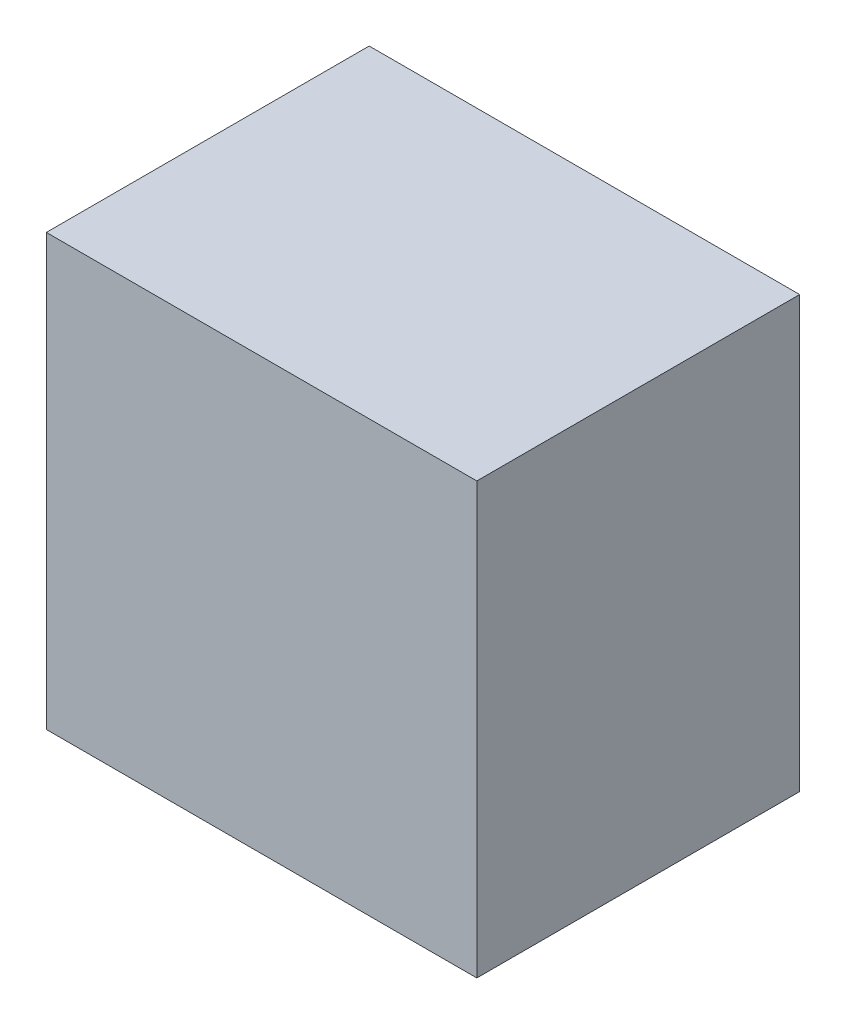
SolidWorks part; units mm, degrees
ref_plane "Front Plane" through (0, 0, 0) normal (0, 0, 1) x (1, 0, 0)
ref_plane "Top Plane" through (0, 0, 0) normal (0, 1, 0) x (1, 0, 0)
ref_plane "Right Plane" through (0, 0, 0) normal (1, 0, 0) x (0, 0, -1)
sketch "Sketch1" plane through (0, 0, 0) normal (0, 0, 1) x (1, 0, 0)
  line L0 (10, 10) -> (-10, 10) construction
  line L1 (10, -10) -> (10, 10) construction
  line L2 (-10, -10) -> (10, -10) construction
  line L3 (-10, 10) -> (-10, -10) construction
  line L4 (10, 10) -> (-10, 10)
  line L5 (10, -10) -> (10, 10)
  line L6 (-10, -10) -> (10, -10)
  line L7 (-10, 10) -> (-10, -10)
extrude "Boss-Extrude1" add sketch "Sketch1" along normal blind 15
ref_plane "Plane1" through (-10, 0, 0) normal (-1, 0, 0) x (0, 0, 1)
